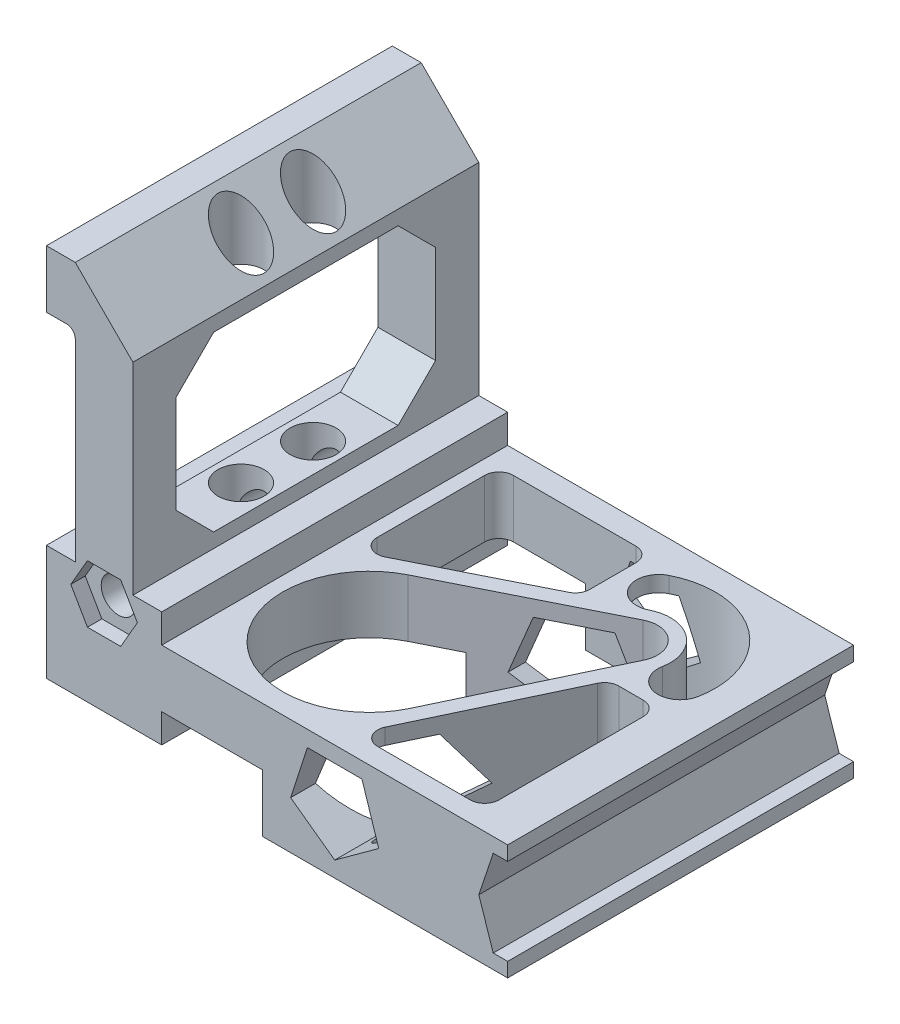
SolidWorks part; units mm, degrees
material "Alloy Steel"
ref_plane "Front Plane" through (0, 0, 0) normal (0, 0, 1) x (1, 0, 0)
ref_plane "Top Plane" through (0, 0, 0) normal (0, 1, 0) x (1, 0, 0)
ref_plane "Right Plane" through (0, 0, 0) normal (1, 0, 0) x (0, 0, -1)
sketch "Sketch1" plane through (0, 0, 0) normal (0, 0, 1) x (1, 0, 0)
  line L0 (0, 0) -> (0, 50.8)
  line L1 (0, 50.8) -> (12.7, 50.8)
  line L2 (12.7, 50.8) -> (12.7, 135.89)
  line L3 (8.89, 139.7) -> (0, 139.7)
  line L4 (0, 139.7) -> (0, 165.1)
  line L5 (0, 165.1) -> (12.7, 165.1)
  line L6 (12.7, 165.1) -> (38.1, 139.7)
  line L7 (38.1, 139.7) -> (38.1, 50.8)
  line L8 (38.1, 50.8) -> (50.8, 50.8)
  line L9 (50.8, 50.8) -> (50.8, 38.1)
  line L10 (50.8, 38.1) -> (203.2, 38.1)
  line L11 (203.2, 38.1) -> (203.2, 31.75)
  line L12 (203.2, 31.75) -> (196.85, 31.75)
  line L13 (196.85, 31.75) -> (190.5, 12.7)
  line L14 (190.5, 12.7) -> (196.85, -6.35)
  line L15 (196.85, -6.35) -> (203.2, -6.35)
  line L16 (0, 0) -> (50.8, 0)
  line L17 (203.2, -12.7) -> (203.2, -6.35)
  line L18 (50.8, 0) -> (50.8, 12.7)
  line L19 (50.8, 12.7) -> (95.25, 12.7)
  line L20 (95.25, 12.7) -> (95.25, -12.7)
  line L21 (95.25, -12.7) -> (203.2, -12.7)
  line L23 (146.4087, 8.2987) -> (138.9952, 31.115)
  line L24 (138.9952, 31.115) -> (115.0048, 31.115)
  line L25 (115.0048, 31.115) -> (107.5913, 8.2987)
  line L26 (107.5913, 8.2987) -> (127, -5.8025)
  line L27 (127, -5.8025) -> (146.4087, 8.2987)
  arc A0 (12.7, 135.89) -> (8.89, 139.7) centre (8.89, 135.89) ccw
  circle A1 centre (25.4, 41.275) radius 7.62
  circle A2 centre (127, 14.605) radius 16.51 construction
  dimension "D1" = 50.8
  dimension "D21" = 3.81
  dimension "D22" = 41.275
  dimension "D24" = 15.24
  dimension "D25" = 16.51
  dimension "D2" = 12.7
  dimension "D3" = 25.4
  dimension "D4" = 50.8
  dimension "D5" = 6.35
  dimension "D6" = 6.35
  dimension "D7" = 25.4
  dimension "D8" = 6.35
  dimension "D9" = 12.7
  dimension "D10" = 12.7
  dimension "D11" = 25.4
  dimension "D12" = 12.7
  dimension "D13" = 50.8
  dimension "D14" = 107.95
  dimension "D15" = 203.2
  dimension "D16" = 165.1
  dimension "D17" = 38.1
  dimension "D18" = 25.4
  dimension "D19" = 12.7
  dimension "D20" = 25.4
  dimension "D23" = 25.4
  dimension "D26" = 27.305
  dimension "D27" = 76.2
extrude "Boss-Extrude1" add sketch "Sketch1" along normal mid plane 152.4
sketch "Sketch2" plane through (0, 38.1, 0) normal (0, 1, 0) x (1, 0, 0)
  line L0 (57.15, 59.69) -> (57.15, 12.3101)
  line L1 (66.3416, 6.6314) -> (120.3166, 33.64)
  line L2 (123.825, 39.3187) -> (123.825, 59.69)
  line L3 (117.475, 66.04) -> (63.5, 66.04)
  line L4 (203.2, 76.2) -> (50.8, 76.2) construction
  line L5 (0, -76.2) -> (0, 76.2) construction
  line L6 (203.2, -76.2) -> (203.2, 76.2) construction
  line L7 (203.2, -76.2) -> (50.8, -76.2) construction
  line L8 (78.2005, 4.8623) -> (147.2851, 39.4317)
  line L9 (129.6888, -45.5066) -> (162.7316, 24.321)
  line L10 (131.2901, -58.2439) -> (161.3387, 5.2561)
  line L11 (167.0785, 8.89) -> (177.8, 8.89)
  line L12 (184.15, 2.54) -> (184.15, -60.96)
  line L13 (177.8, -67.31) -> (137.0299, -67.31)
  arc A0 (78.2005, 4.8623) -> (129.6888, -45.5066) centre (95.25, -29.21) ccw
  arc A1 (162.7316, 24.321) -> (147.2851, 39.4317) centre (152.4, 29.21) ccw
  arc A2 (184.15, -60.96) -> (177.8, -67.31) centre (177.8, -60.96) cw
  arc A3 (131.2901, -58.2439) -> (137.0299, -67.31) centre (137.0299, -60.96) ccw
  arc A4 (177.8, 8.89) -> (184.15, 2.54) centre (177.8, 2.54) cw
  arc A5 (161.3387, 5.2561) -> (167.0785, 8.89) centre (167.0785, 2.54) cw
  arc A6 (120.3166, 33.64) -> (123.825, 39.3187) centre (117.475, 39.3187) ccw
  arc A7 (123.825, 59.69) -> (117.475, 66.04) centre (117.475, 59.69) ccw
  arc A8 (57.15, 59.69) -> (63.5, 66.04) centre (63.5, 59.69) cw
  arc A9 (57.15, 12.3101) -> (66.3416, 6.6314) centre (63.5, 12.3101) ccw
  arc A10 (178.9051, 24.13) -> (140.3141, 53.34) centre (152.4, 29.21) ccw construction
  arc A11 (188.5716, 22.2773) -> (135.9063, 62.1404) centre (152.4, 29.21) ccw
  arc A12 (169.2385, 25.9827) -> (144.7219, 44.5396) centre (152.4, 29.21) ccw
  arc A13 (135.9063, 62.1404) -> (144.7219, 44.5396) centre (140.3141, 53.34) ccw
  arc A14 (169.2385, 25.9827) -> (188.5716, 22.2773) centre (178.9051, 24.13) ccw
  point P26 (127, -67.31)
  point P39 (57.15, 2.032)
  dimension "D5" = 107.95
  dimension "D7" = 76.2
  dimension "D10" = 22.86
  dimension "D15" = 6.35
  dimension "D16" = 73.66
  dimension "D17" = 34.29
  dimension "D18" = 53.975
  dimension "D19" = 26.9875
  dimension "D1" = 10.16
  dimension "D2" = 64.008
  dimension "D3" = 123.825
  dimension "D4" = 57.15
  dimension "D6" = 46.99
  dimension "D8" = 105.41
  dimension "D9" = 50.8
  dimension "D11" = 8.89
  dimension "D12" = 19.05
  dimension "D13" = 76.2
  dimension "D14" = 85.09
  dimension "D20" = 100.33
  dimension "D21" = 129.54
extrude "Cut-Extrude1" cut sketch "Sketch2" against normal through all
sketch "Sketch3" plane through (38.1, 0, 0) normal (1, 0, 0) x (0, 0, -1)
  line L0 (-76.2, 165.1) -> (76.2, 165.1) construction
  line L1 (-40.64, 133.35) -> (40.64, 133.35)
  line L2 (-57.15, 116.84) -> (-57.15, 73.66)
  line L3 (-40.64, 57.15) -> (40.64, 57.15)
  line L4 (57.15, 116.84) -> (57.15, 73.66)
  line L5 (-57.15, 133.35) -> (57.15, 57.15) construction
  line L6 (-57.15, 57.15) -> (57.15, 133.35) construction
  line L7 (-76.2, 50.8) -> (-76.2, 139.7) construction
  line L8 (-57.15, 116.84) -> (-40.64, 133.35)
  line L9 (-57.15, 73.66) -> (-40.64, 57.15)
  line L10 (40.64, 57.15) -> (57.15, 73.66)
  line L11 (40.64, 133.35) -> (57.15, 116.84)
  point P0 (0, 95.25)
  dimension "D1" = 76.2
  dimension "D2" = 31.75
  dimension "D3" = 114.3
  dimension "D4" = 19.05
extrude "Cut-Extrude2" cut sketch "Sketch3" against normal through all
sketch "Sketch4" plane through (0, 0, 0) normal (0, -1, 0) x (1, 0, 0)
  line L0 (0, 76.2) -> (50.8, 76.2) construction
  circle A0 centre (25.4, 15.875) radius 10.16
  circle A1 centre (25.4, -15.875) radius 10.16
  point P9 (25.4, 76.2)
  dimension "D1" = 20.32
  dimension "D2" = 20.32
  dimension "D3" = 31.75
  dimension "D4" = 60.325
extrude "Cut-Extrude3" cut sketch "Sketch4" against normal through all
sketch "Sketch6" plane through (0, 0, 0) normal (0, -1, 0) x (1, 0, 0)
  line L0 (50.8, 76.2) -> (50.8, -76.2) construction
  line L1 (25.4, 0.762) -> (36.0865, 5.1885)
  line L2 (36.0865, 5.1885) -> (40.513, 15.875)
  line L3 (40.513, 15.875) -> (36.0865, 26.5615)
  line L4 (36.0865, 26.5615) -> (25.4, 30.988)
  line L5 (25.4, 30.988) -> (14.7135, 26.5615)
  line L6 (14.7135, 26.5615) -> (10.287, 15.875)
  line L7 (10.287, 15.875) -> (14.7135, 5.1885)
  line L8 (14.7135, 5.1885) -> (25.4, 0.762)
  line L9 (25.4, -30.988) -> (36.0865, -26.5615)
  line L10 (36.0865, -26.5615) -> (40.513, -15.875)
  line L11 (40.513, -15.875) -> (36.0865, -5.1885)
  line L12 (36.0865, -5.1885) -> (25.4, -0.762)
  line L13 (25.4, -0.762) -> (14.7135, -5.1885)
  line L14 (14.7135, -5.1885) -> (10.287, -15.875)
  line L15 (10.287, -15.875) -> (14.7135, -26.5615)
  line L16 (14.7135, -26.5615) -> (25.4, -30.988)
  line L17 (50.8, 76.2) -> (50.8, -76.2) construction
  circle A0 centre (25.4, 15.875) radius 13.9626 construction
  circle A1 centre (25.4, -15.875) radius 13.9626 construction
  dimension "D1" = 30.226
  dimension "D2" = 30.226
  dimension "D3" = 22.5
  dimension "D4" = 22.5
extrude "Cut-Extrude4" cut sketch "Sketch6" against normal blind 4.445
sketch "Sketch7" plane through (0, 0, 76.2) normal (0, 0, 1) x (1, 0, 0)
  line L1 (40.0647, 41.275) -> (32.7323, 53.975)
  line L2 (32.7323, 53.975) -> (18.0677, 53.975)
  line L3 (18.0677, 53.975) -> (10.7353, 41.275)
  line L4 (10.7353, 41.275) -> (18.0677, 28.575)
  line L5 (18.0677, 28.575) -> (32.7323, 28.575)
  line L6 (32.7323, 28.575) -> (40.0647, 41.275)
  circle A0 centre (25.4, 41.275) radius 12.7 construction
  dimension "D1" = 25.4
extrude "Cut-Extrude5" cut sketch "Sketch7" against normal blind 6.35
mirror "Mirror1" about plane through (0, 0, 0) normal (0, 0, 1) of "Cut-Extrude5"
equation "\"D2@Sketch6\"=\"D1@Sketch6\""
